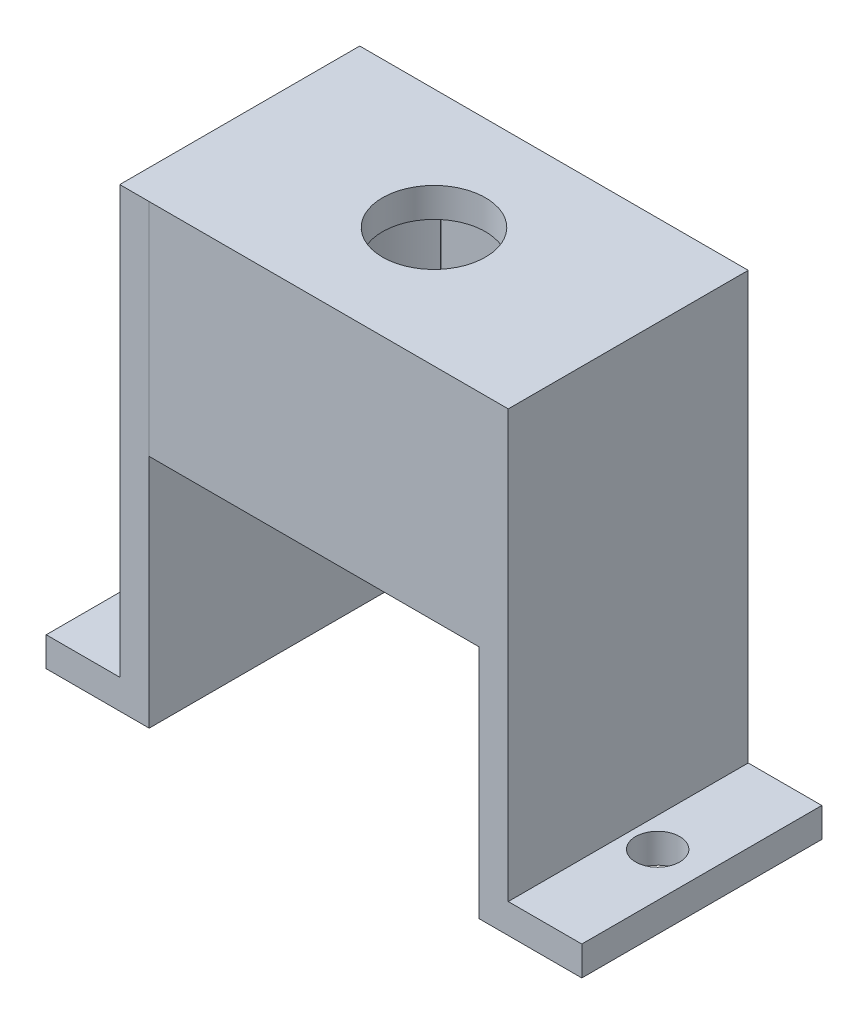
SolidWorks part; units mm, degrees
ref_plane "Front Plane" through (0, 0, 0) normal (0, 0, 1) x (1, 0, 0)
ref_plane "Top Plane" through (0, 0, 0) normal (0, 1, 0) x (1, 0, 0)
ref_plane "Right Plane" through (0, 0, 0) normal (1, 0, 0) x (0, 0, -1)
sketch "Çizim1" plane through (0, 0, 0) normal (0, 1, 0) x (1, 0, 0)
  line L5 (-24.27, 9.2305) -> (-10.2731, 9.2334)
  line L9 (-24.2789, -5.7598) -> (-10.271, -5.7598)
  arc A0 (-24.2789, 9.2402) -> (-24.2789, -5.7598) centre (-17.4292, 1.7402) ccw construction
  arc A5 (-24.2877, 9.2499) -> (-24.2877, -5.7695) centre (-17.4292, 1.7402) ccw
  arc A7 (-24.27, 9.2305) -> (-24.27, -5.7501) centre (-17.4292, 1.7402) ccw
  arc A8 (-24.27, 9.2305) -> (-24.2877, 9.2499) centre (-24.2789, 9.2402) ccw
  arc A9 (-24.2877, -5.7695) -> (-24.27, -5.7501) centre (-24.2789, -5.7598) ccw
  arc A10 (-10.2665, 9.2402) -> (-10.271, -5.7598) centre (-17.5944, 1.7424) cw construction
  arc A11 (-10.2644, -5.7666) -> (-10.2599, 9.2469) centre (-17.5944, 1.7424) ccw
  arc A12 (-10.2776, -5.7531) -> (-10.2731, 9.2334) centre (-17.5944, 1.7424) ccw
  arc A13 (-10.2776, -5.7531) -> (-10.2644, -5.7666) centre (-10.271, -5.7598) ccw
  arc A14 (-10.2599, 9.2469) -> (-10.2731, 9.2334) centre (-10.2665, 9.2402) ccw
  point P2 (-27.5864, 1.7402)
  point P14 (-7.1104, 1.7392)
extrude "Yükseklik-Ekstrüzyon1" add sketch "Çizim1" along normal blind 12 contours A13 A12 L5 A7 A9 L9
sketch "Çizim2" plane through (0, 12, 0) normal (0, 1, 0) x (1, 0, 0)
  line L4 (-24.9729, -6.3716) -> (-28.4729, -6.3716)
  line L5 (-9.566, 9.9405) -> (-6.066, 9.9405)
  line L7 (-28.4729, -6.3716) -> (-6.066, -6.3716)
  line L8 (-28.4729, -6.3716) -> (-28.4729, 9.9405)
  line L9 (-28.4729, 9.9405) -> (-6.066, 9.9405)
  line L10 (-6.066, -6.3716) -> (-6.066, 9.9405)
  arc M1 (-10.2804, -5.7598) -> (-10.2776, -5.7531) centre (-10.271, -5.7598) cw
  arc M2 (-10.2776, -5.7531) -> (-10.2731, 9.2334) centre (-17.5944, 1.7424) ccw
  line M3 (-10.2731, 9.2334) -> (-24.27, 9.2305)
  arc M4 (-24.27, 9.2305) -> (-24.27, -5.7501) centre (-17.4292, 1.7402) ccw
  arc M5 (-24.27, -5.7501) -> (-24.2657, -5.7598) centre (-24.2789, -5.7598) cw
  line M6 (-24.2657, -5.7598) -> (-10.2804, -5.7598)
extrude "Yükseklik-Ekstrüzyon3" add sketch "Çizim2" against normal blind 15 contours L7 L10 L5 L9 L8 L4 M1 M6 M5 M4 M3 M2
sketch "Çizim5" plane through (0, 0, 0) normal (0, 1, 0) x (1, 0, 0)
  line L0 (-24.27, -5.7501) -> (-10.2804, -5.7598)
  line L1 (-10.2607, 9.246) -> (-24.27, 9.2305)
  arc A0 (-10.2607, 9.246) -> (-10.2804, -5.7598) centre (-17.4169, 1.7525) cw construction
  arc A5 (-24.27, -5.7501) -> (-24.27, 9.2305) centre (-17.4292, 1.7402) cw construction
  arc A6 (-24.2865, 9.2486) -> (-24.2865, -5.7682) centre (-17.4292, 1.7402) ccw
  arc A7 (-24.2535, 9.2124) -> (-24.2535, -5.732) centre (-17.4292, 1.7402) ccw
  arc A8 (-24.2535, 9.2124) -> (-24.2865, 9.2486) centre (-24.27, 9.2305) ccw
  arc A9 (-24.2865, -5.7682) -> (-24.2535, -5.732) centre (-24.27, -5.7501) ccw
  arc A10 (-10.28, -5.7603) -> (-10.2602, 9.2465) centre (-17.4169, 1.7525) ccw
  arc A11 (-10.2809, -5.7593) -> (-10.2612, 9.2455) centre (-17.4169, 1.7525) ccw
  arc A12 (-10.2809, -5.7593) -> (-10.28, -5.7603) centre (-10.2804, -5.7598) ccw
  arc A13 (-10.2602, 9.2465) -> (-10.2612, 9.2455) centre (-10.2607, 9.246) ccw
  point P5 (-7.0553, 1.7389)
  point P16 (-27.5732, 1.7402)
extrude "Kes-Ekstrüzyon2" cut sketch "Çizim5" along normal blind 10 contours A13 L1 A8 A7 A9 L0 A12 A11
sketch "Çizim7" plane through (0, 12, 0) normal (0, 1, 0) x (1, 0, 0)
  line L0 (-28.4729, 9.9405) -> (-6.066, -6.3716) construction
  circle A0 centre (-17.2694, 1.7845) radius 3.5
extrude "Kes-Ekstrüzyon3" cut sketch "Çizim7" against normal blind 10 contours A0
sketch "Çizim8" plane through (-28.4729, 0, 0) normal (-1, 0, 0) x (0, 0, 1)
  line L0 (-9.9405, 12) -> (-9.9405, -19) construction
  point P3 (0, 0)
sketch "Çizim9" plane through (-28.4729, 0, 0) normal (-1, 0, 0) x (0, 0, 1)
  line L1 (-9.9405, 12) -> (6.3695, 12)
  line L2 (-9.9405, 12) -> (-9.9405, -19)
  line L3 (-9.9405, -19) -> (6.3695, -19)
  line L4 (6.3695, 12) -> (6.3695, -19)
  point P5 (0, 0)
  point P6 (0, 0)
extrude "Yükseklik-Ekstrüzyon4" add sketch "Çizim9" along normal blind 2
sketch "Çizim11" plane through (-6.066, 0, 0) normal (1, 0, 0) x (0, 0, -1)
  line L1 (-6.3716, 12) -> (9.9405, 12)
  line L2 (-6.3716, 12) -> (-6.3716, -19)
  line L3 (-6.3716, -19) -> (9.9405, -19)
  line L4 (9.9405, 12) -> (9.9405, -19)
extrude "Yükseklik-Ekstrüzyon5" add sketch "Çizim11" along normal blind 2
sketch "Çizim12" plane through (-4.066, 0, 0) normal (1, 0, 0) x (0, 0, -1)
  line L0 (9.9405, 12) -> (9.9405, -19) construction
  line L1 (-6.3716, -19) -> (9.9405, -19)
  line L2 (-6.3716, -19) -> (-6.3716, -17)
  line L3 (-6.3716, -17) -> (9.9405, -17)
  line L4 (9.9405, -19) -> (9.9405, -17)
extrude "Yükseklik-Ekstrüzyon6" add sketch "Çizim12" along normal blind 5
sketch "Çizim13" plane through (-30.4729, 0, 0) normal (-1, 0, 0) x (0, 0, 1)
  line L0 (6.3695, -19) -> (6.3695, 12) construction
  line L1 (-9.9405, -19) -> (6.3695, -19)
  line L2 (-9.9405, -19) -> (-9.9405, -17)
  line L3 (-9.9405, -17) -> (6.3695, -17)
  line L4 (6.3695, -19) -> (6.3695, -17)
extrude "Yükseklik-Ekstrüzyon7" add sketch "Çizim13" along normal blind 5
sketch "Çizim16" plane through (0, -19, 0) normal (0, -1, 0) x (1, 0, 0)
  circle A0 centre (-32.4729, -1.7855) radius 1.5
  circle A1 centre (-2.066, -1.7845) radius 1.5
extrude "Kes-Ekstrüzyon4" cut sketch "Çizim16" against normal blind 5
